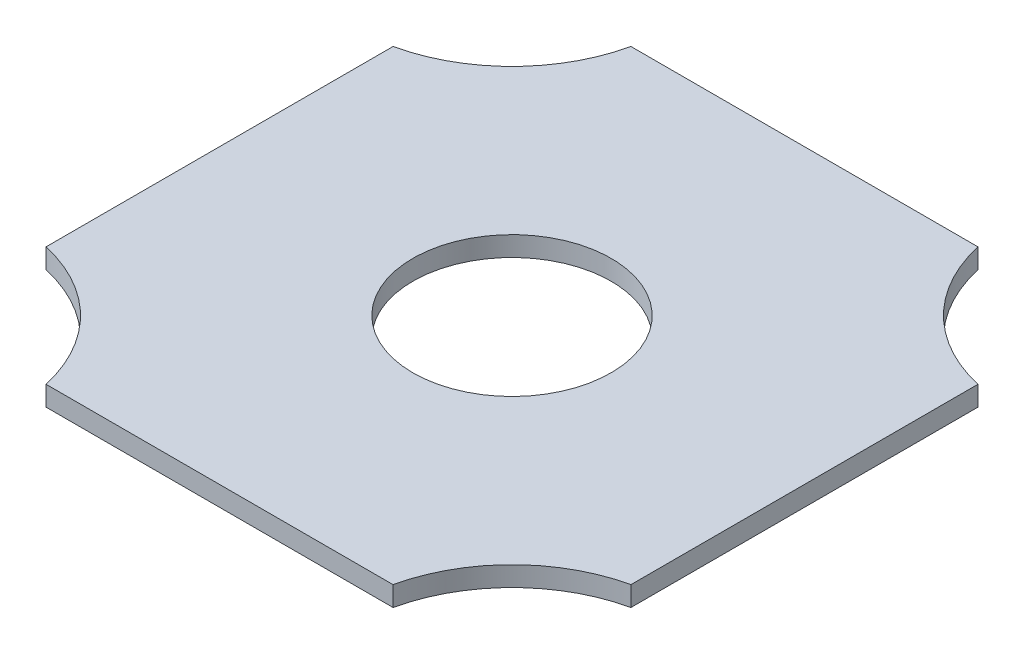
SolidWorks part; units mm, degrees
ref_plane "Front Plane" through (0, 0, 0) normal (0, 0, 1) x (1, 0, 0)
ref_plane "Top Plane" through (0, 0, 0) normal (0, 1, 0) x (1, 0, 0)
ref_plane "Right Plane" through (0, 0, 0) normal (1, 0, 0) x (0, 0, -1)
sketch "Sketch1" plane through (0, 0, 0) normal (0, 1, 0) x (1, 0, 0)
  line L0 (-28.7605, 18.5352) -> (-28.7605, -16.4648)
  line L1 (-16.7605, -28.4648) -> (18.2395, -28.4648)
  line L2 (30.2395, -16.4648) -> (30.2395, 18.5352)
  line L3 (18.2395, 30.5352) -> (-16.7605, 30.5352)
  arc A0 (-28.7605, 18.5352) -> (-16.7605, 30.5352) centre (-32.227, 34.0017) ccw
  arc A1 (-16.7605, -28.4648) -> (-28.7605, -16.4648) centre (-32.227, -31.9312) ccw
  arc A2 (30.2395, -16.4648) -> (18.2395, -28.4648) centre (33.7059, -31.9312) ccw
  arc A3 (18.2395, 30.5352) -> (30.2395, 18.5352) centre (33.7059, 34.0017) ccw
extrude "Boss-Extrude1" add sketch "Sketch1" along normal blind 2
sketch "Sketch6" plane through (0, 2, 0) normal (0, 1, 0) x (1, 0, 0)
  circle A0 centre (0.7395, 1.0352) radius 10
  dimension "D2" = 20
extrude "Cut-Extrude1" cut sketch "Sketch6" against normal blind 3
